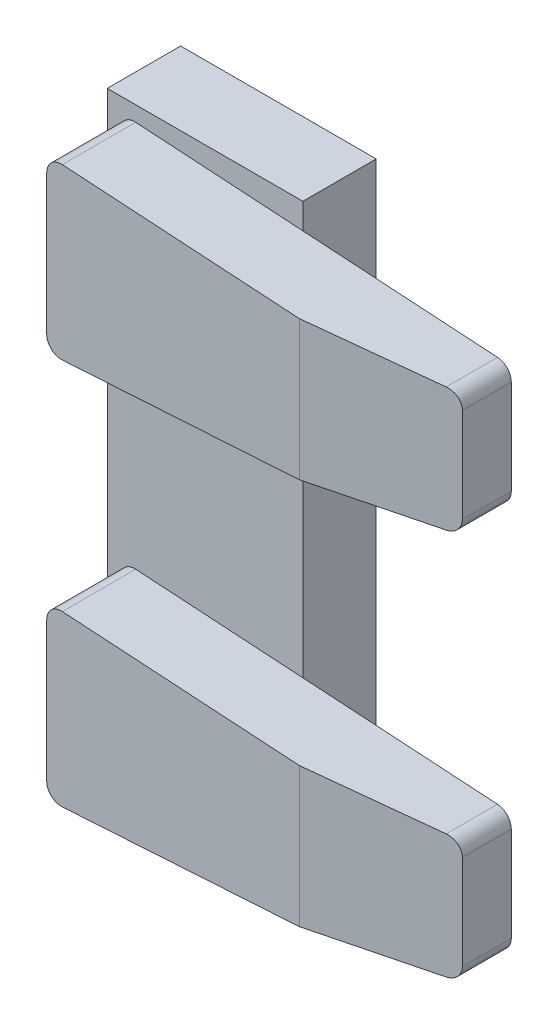
SolidWorks part; units mm, degrees
ref_plane "Front Plane" through (0, 0, 0) normal (0, 0, 1) x (1, 0, 0)
ref_plane "Top Plane" through (0, 0, 0) normal (0, 1, 0) x (1, 0, 0)
ref_plane "Right Plane" through (0, 0, 0) normal (1, 0, 0) x (0, 0, -1)
sketch "Sketch1" plane through (0, 0, 0) normal (0, 0, 1) x (1, 0, 0)
  line L1 (-45.2504, 220.2598) -> (-5.2504, 220.2598)
  line L2 (-45.2504, 220.2598) -> (-45.2504, 340.2598)
  line L3 (-45.2504, 340.2598) -> (-5.2504, 340.2598)
  line L4 (-5.2504, 220.2598) -> (-5.2504, 340.2598)
  line L5 (-45.2504, 220.2598) -> (-5.2504, 340.2598) construction
  line L6 (-45.2504, 340.2598) -> (-5.2504, 220.2598) construction
  point P0 (-25.2504, 280.2598)
  point P5 (-25.1096, 278.9785)
  point P6 (-27.1318, 277.5714)
  point P7 (-25.2504, 280.2598)
  dimension "D1" = 120
  dimension "D2" = 40
extrude "Boss-Extrude1" add sketch "Sketch1" along normal blind 15
sketch "Sketch2" plane through (0, 0, 15) normal (0, 0, 1) x (1, 0, 0)
  line L0 (-42.6349, 258.2053) -> (-42.6349, 223.2053)
  line L1 (-42.6349, 223.2053) -> (37.3651, 228.2053)
  line L2 (37.3651, 228.2053) -> (37.3651, 253.2053)
  line L3 (37.3651, 253.2053) -> (-42.6349, 258.2053)
  line L4 (-42.6349, 240.7053) -> (37.3651, 240.7053) construction
  line L5 (-42.6349, 337.3532) -> (-42.6349, 302.3532)
  line L6 (-42.6349, 302.3532) -> (37.3651, 307.3532)
  line L7 (37.3651, 307.3532) -> (37.3651, 332.3532)
  line L8 (37.3651, 332.3532) -> (-42.6349, 337.3532)
  line L9 (-42.6349, 319.8532) -> (37.3651, 319.8532) construction
  point P6 (37.4302, 225.7391)
  point P7 (37.8647, 228.3463)
  point P8 (-42.7419, 241.0671)
  point P9 (-41.6881, 240.9513)
  point P10 (-41.094, 240.7053)
  point P17 (-43.123, 315.5806)
  point P18 (-42.9294, 311.9993)
  point P19 (67.695, 281.1456)
  point P20 (-42.6349, 302.3532)
  dimension "D1" = 35
  dimension "D2" = 80
  dimension "D3" = 25
  dimension "D4" = 35
  dimension "D5" = 25
extrude "Boss-Extrude2" add sketch "Sketch2" along normal blind 15 separate body
chamfer "Chamfer1" distance 5 angle 80 1 edges at (37.3651, 319.8532, 30)
chamfer "Chamfer2" distance 5 angle 80 1 edges at (37.3651, 240.7053, 30)
fillet "Fillet1" radius 3 4 edges at (-42.6349, 258.2053, 22.5) (-42.6349, 223.2053, 22.5) (37.3651, 228.2053, 20) (37.3651, 253.2053, 20)
fillet "Fillet2" radius 3 4 edges at (-42.6349, 302.3532, 22.5) (-42.6349, 337.3532, 22.5) (37.3651, 332.3532, 20) (37.3651, 307.3532, 20)
